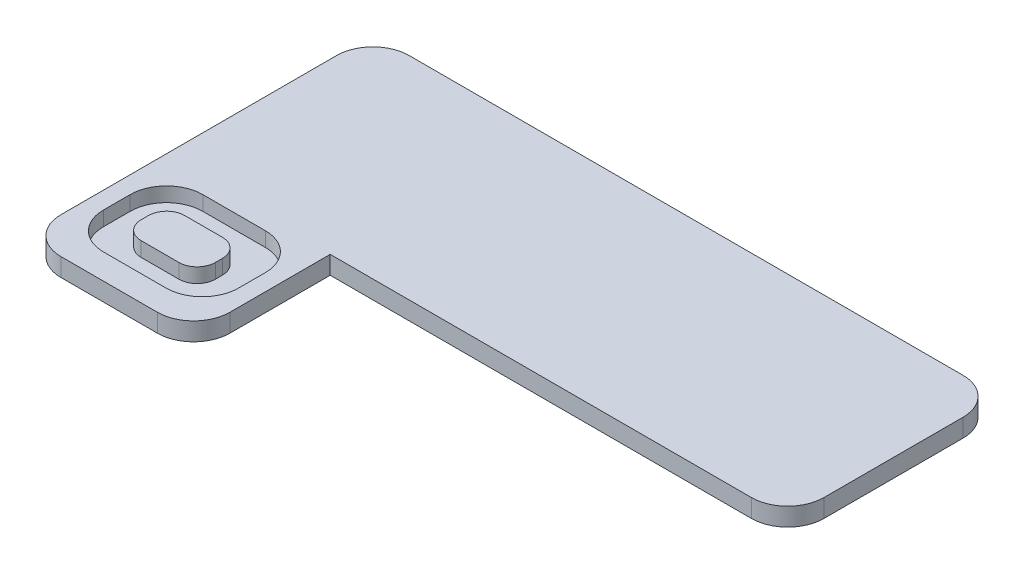
SolidWorks part; units mm, degrees
ref_plane "Front Plane" through (0, 0, 0) normal (0, 0, 1) x (1, 0, 0)
ref_plane "Top Plane" through (0, 0, 0) normal (0, 1, 0) x (1, 0, 0)
ref_plane "Right Plane" through (0, 0, 0) normal (1, 0, 0) x (0, 0, -1)
sketch "Sketch1" plane through (0, 0, 0) normal (0, 1, 0) x (1, 0, 0)
  line L0 (2.54, 0) -> (41.3048, 0)
  line L1 (43.8448, -2.54) -> (43.8448, -12.274)
  line L2 (41.3048, -14.814) -> (11.8273, -14.814)
  line L3 (0, -14.814) -> (0, -2.54)
  line L4 (0, -14.814) -> (0, -21.8315)
  line L5 (2.54, -24.3715) -> (9.2873, -24.3715)
  line L6 (11.8273, -21.8315) -> (11.8273, -14.814)
  arc A0 (0, -21.8315) -> (2.54, -24.3715) centre (2.54, -21.8315) ccw
  arc A1 (9.2873, -24.3715) -> (11.8273, -21.8315) centre (9.2873, -21.8315) ccw
  arc A2 (43.8448, -12.274) -> (41.3048, -14.814) centre (41.3048, -12.274) cw
  arc A3 (41.3048, 0) -> (43.8448, -2.54) centre (41.3048, -2.54) cw
  arc A4 (2.54, 0) -> (0, -2.54) centre (2.54, -2.54) ccw
  point P18 (0, 0)
  dimension "D1" = 2.54
extrude "Boss-Extrude1" add sketch "Sketch1" along normal blind 1.27
sketch "Sketch2" plane through (0, 1.27, 0) normal (0, 1, 0) x (1, 0, 0)
  line L0 (8.1252, -15.6496) -> (3.7446, -15.6496)
  line L1 (1.2046, -18.1896) -> (1.2046, -20.0615)
  line L2 (3.7446, -22.6015) -> (8.1252, -22.6015)
  line L3 (10.6652, -20.0615) -> (10.6652, -18.1896)
  line L5 (4.3849, -17.5528) -> (7.0301, -17.5528)
  line L6 (3.1149, -18.8228) -> (3.1149, -19.3302)
  line L7 (4.3849, -20.6002) -> (7.0301, -20.6002)
  line L8 (8.3001, -18.8228) -> (8.3001, -19.3302)
  arc A0 (1.2046, -20.0615) -> (3.7446, -22.6015) centre (3.7446, -20.0615) ccw
  arc A1 (8.1252, -22.6015) -> (10.6652, -20.0615) centre (8.1252, -20.0615) ccw
  arc A2 (8.1252, -15.6496) -> (10.6652, -18.1896) centre (8.1252, -18.1896) cw
  arc A3 (3.7446, -15.6496) -> (1.2046, -18.1896) centre (3.7446, -18.1896) ccw
  arc A4 (3.1149, -19.3302) -> (4.3849, -20.6002) centre (4.3849, -19.3302) ccw
  arc A5 (7.0301, -20.6002) -> (8.3001, -19.3302) centre (7.0301, -19.3302) ccw
  arc A6 (7.0301, -17.5528) -> (8.3001, -18.8228) centre (7.0301, -18.8228) cw
  arc A7 (4.3849, -17.5528) -> (3.1149, -18.8228) centre (4.3849, -18.8228) ccw
  dimension "D1" = 2.54
  dimension "D2" = 1.27
extrude "Cut-Extrude1" cut sketch "Sketch2" against normal blind 1.016
